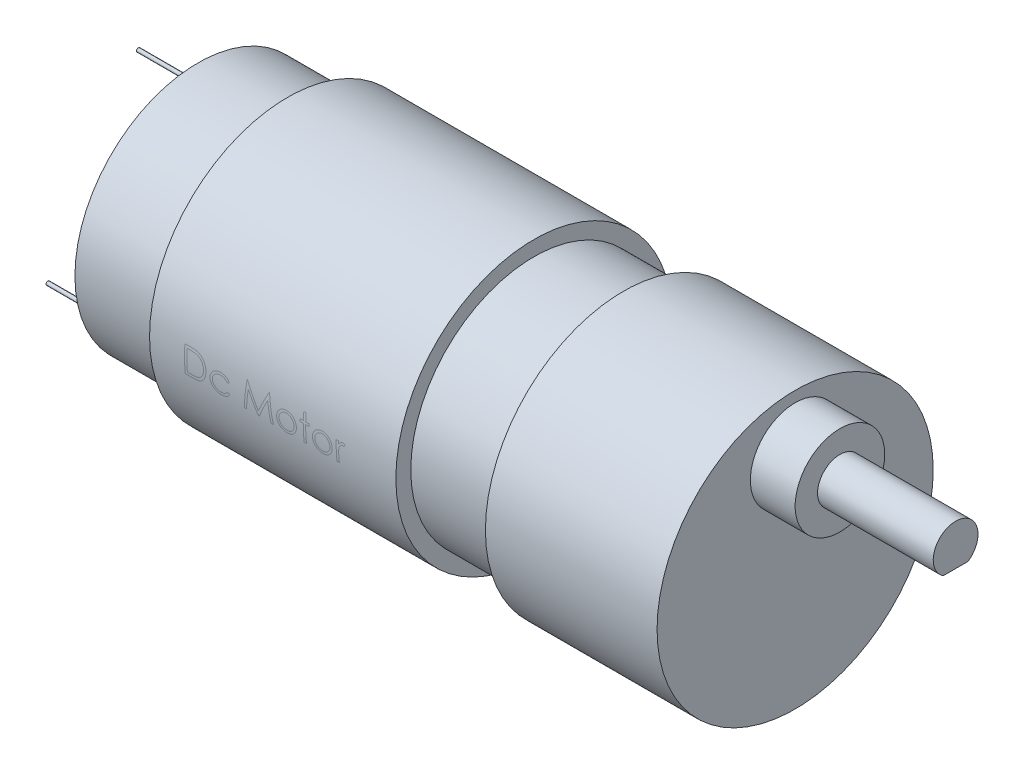
SolidWorks part; units mm, degrees
ref_plane "Front Plane" through (0, 0, 0) normal (0, 0, 1) x (1, 0, 0)
ref_plane "Top Plane" through (0, 0, 0) normal (0, 1, 0) x (1, 0, 0)
ref_plane "Right Plane" through (0, 0, 0) normal (1, 0, 0) x (0, 0, -1)
sketch "Sketch2" plane through (0, 0, 0) normal (0, 0, 1) x (1, 0, 0)
  line L0 (17.6825, 31.4946) -> (88.4123, 31.4946) construction
  line L1 (88, 0) -> (88, 18.5)
  line L2 (88, 18.5) -> (65, 18.5)
  line L3 (65, 18.5) -> (65, 16.5)
  line L4 (65, 16.5) -> (53, 16.5)
  line L5 (53, 16.5) -> (53, 18.5)
  line L6 (53, 18.5) -> (20, 18.5)
  line L7 (20, 18.5) -> (20, 16.5)
  line L8 (20, 16.5) -> (8, 16.5)
  line L9 (8, 16.5) -> (8, 8)
  line L10 (8, 8) -> (4, 8)
  line L11 (4, 8) -> (4, 2)
  line L12 (4, 2) -> (0, 2)
  line L13 (0, 2) -> (0, 0)
  line L14 (0, 0) -> (88, 0) construction
  line L15 (88, 0) -> (0, 0)
  dimension "D1" = 23
  dimension "D2" = 37
  dimension "D3" = 65
  dimension "D4" = 57
  dimension "D5" = 16
  dimension "D6" = 12
  dimension "D7" = 12
  dimension "D8" = 2
  dimension "D9" = 4
  dimension "D10" = 2
revolve "Revolve1" add sketch "Sketch2" angle 360 about L15
sketch "Sketch3" plane through (88, 0, 0) normal (1, 0, 0) x (0, 0, -1)
  circle A0 centre (0, 11.0563) radius 6
  dimension "D1" = 12
extrude "Boss-Extrude1" add sketch "Sketch3" along normal blind 6
sketch "Sketch4" plane through (94, 0, 0) normal (1, 0, 0) x (0, 0, -1)
  circle A0 centre (0, 11.0563) radius 3
  dimension "D1" = 6
extrude "Boss-Extrude2" add sketch "Sketch4" along normal blind 3.5
sketch "Sketch5" plane through (97.5, 0, 0) normal (1, 0, 0) x (0, 0, -1)
  line L0 (1.6583, 8.5563) -> (-1.6583, 8.5563)
  circle A0 centre (0, 11.0563) radius 3 construction
  arc A1 (1.6583, 8.5563) -> (-1.6583, 8.5563) centre (0, 11.0563) ccw
  point P6 (0, 8.0563)
  dimension "D1" = 0.5
extrude "Boss-Extrude3" add sketch "Sketch5" along normal blind 12
sketch "Sketch6" plane through (8, 0, 0) normal (-1, 0, 0) x (0, 0, 1)
  circle A0 centre (0, 14) radius 0.25
  circle A1 centre (12.1244, -7) radius 0.25
  circle A2 centre (-12.1244, -7) radius 0.25
  point P9 (0, 0)
  dimension "D1" = 0.5
  dimension "D2" = 14
  dimension "D3" = 3
extrude "Boss-Extrude4" add sketch "Sketch6" along normal up to surface (8 mm away) up to face at (0, 0, -2)
ref_plane "Plane1" through (0, 0, 20) normal (0, 0, 1) x (1, 0, 0)
sketch "Sketch7" plane through (0, 0, 20) normal (0, 0, 1) x (1, 0, 0)
  text T0 "Dc Motor"
split line "Split Line1"
